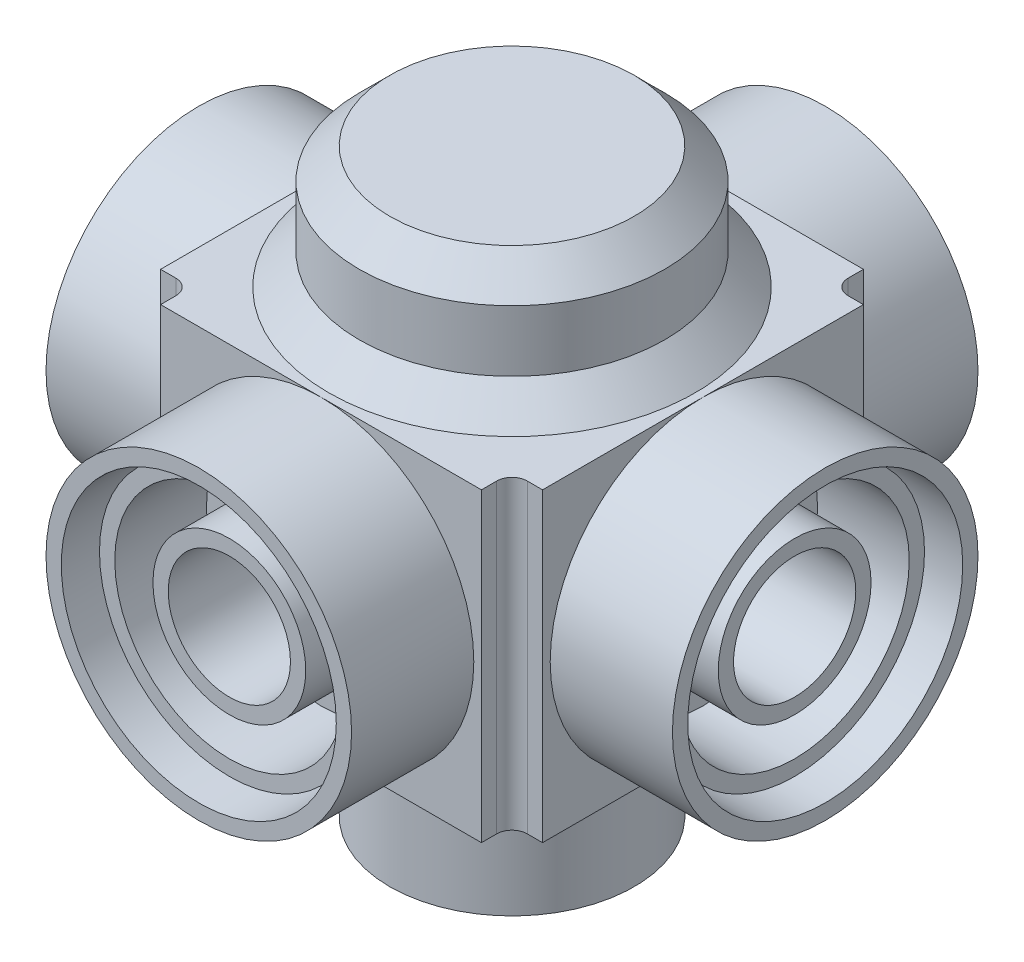
SolidWorks part; units mm, degrees
material "Ti-6Al-4VSolution treated and aged (SS)"
ref_plane "Front Plane" through (0, 0, 0) normal (0, 0, 1) x (1, 0, 0)
ref_plane "Top Plane" through (0, 0, 0) normal (0, 1, 0) x (1, 0, 0)
ref_plane "Right Plane" through (0, 0, 0) normal (1, 0, 0) x (0, 0, -1)
sketch "Sketch1" plane through (0, 0, 0) normal (0, 1, 0) x (1, 0, 0)
  circle A0 centre (0, 0) radius 100
  dimension "D1" = 200
extrude "Boss-Extrude1" add sketch "Sketch1" against normal blind 80
sketch "Sketch2" plane through (0, -80, 0) normal (0, -1, 0) x (1, 0, 0)
  line L1 (125, 125) -> (-125, 125)
  line L2 (125, 125) -> (125, -125)
  line L3 (125, -125) -> (-125, -125)
  line L4 (-125, 125) -> (-125, -125)
  line L5 (125, 125) -> (-125, -125) construction
  line L6 (125, -125) -> (-125, 125) construction
  point P0 (0, 0)
  dimension "D1" = 250
  dimension "D2" = 250
extrude "Boss-Extrude2" add sketch "Sketch2" along normal blind 200
sketch "Sketch3" plane through (0, -280, 0) normal (0, -1, 0) x (1, 0, 0)
  circle A0 centre (0, 0) radius 80
  circle A1 centre (0, 0) radius 70
  dimension "D1" = 160
  dimension "D2" = 140
extrude "Boss-Extrude3" add sketch "Sketch3" along normal blind 100
chamfer "Chamfer1" distance 20 angle 45 2 edges at (0, -80, 100) (0, 0, 100)
sketch "Sketch4" plane through (125, 0, 0) normal (1, 0, 0) x (0, 0, -1)
  line L0 (125, -280) -> (-125, -280) construction
  line L1 (-125, -80) -> (-105, -80)
  line L2 (-125, -80) -> (-125, -280)
  line L3 (-125, -280) -> (-105, -280)
  line L4 (-105, -80) -> (-105, -280)
  line L6 (125, -80) -> (105, -80)
  line L7 (125, -80) -> (125, -280)
  line L8 (125, -280) -> (105, -280)
  line L9 (105, -80) -> (105, -280)
  dimension "D1" = 20
  dimension "D2" = 20
extrude "Cut-Extrude1" cut sketch "Sketch4" against normal blind 20
sketch "Sketch5" plane through (125, 0, 0) normal (1, 0, 0) x (0, 0, -1)
  circle A0 centre (0, -180) radius 100
  circle A1 centre (0, -180) radius 90
  dimension "D1" = 200
  dimension "D3" = 180
  dimension "D2" = 180
extrude "Boss-Extrude4" add sketch "Sketch5" along normal blind 80
sketch "Sketch6" plane through (125, 0, 0) normal (1, 0, 0) x (0, 0, -1)
  circle A0 centre (0, -180) radius 85
  circle A1 centre (0, -180) radius 75
  circle A2 centre (0, -180) radius 50
  circle A3 centre (0, -180) radius 40
  dimension "D1" = 170
  dimension "D2" = 150
  dimension "D3" = 100
  dimension "D4" = 80
extrude "Boss-Extrude5" add sketch "Sketch6" along normal blind 60 contours A0 A1 | A2 A3
pattern_circular "CirPattern1" count 4 over 360 about axis through (0, 0, 0) along (0, 1, 0) of "Boss-Extrude4", "Boss-Extrude5", "Cut-Extrude1"
fillet "Fillet1" radius 10 4 edges at (-105, -180, 105) (105, -180, 105) (105, -180, -105) (-105, -180, -105)
sketch "Sketch7" plane through (0, 0, 0) normal (0, 0, 1) x (1, 0, 0)
  circle A0 centre (0, -330) radius 12.5
  dimension "D1" = 25
  dimension "D2" = 330
extrude "Cut-Extrude2" cut sketch "Sketch7" against normal blind 123
